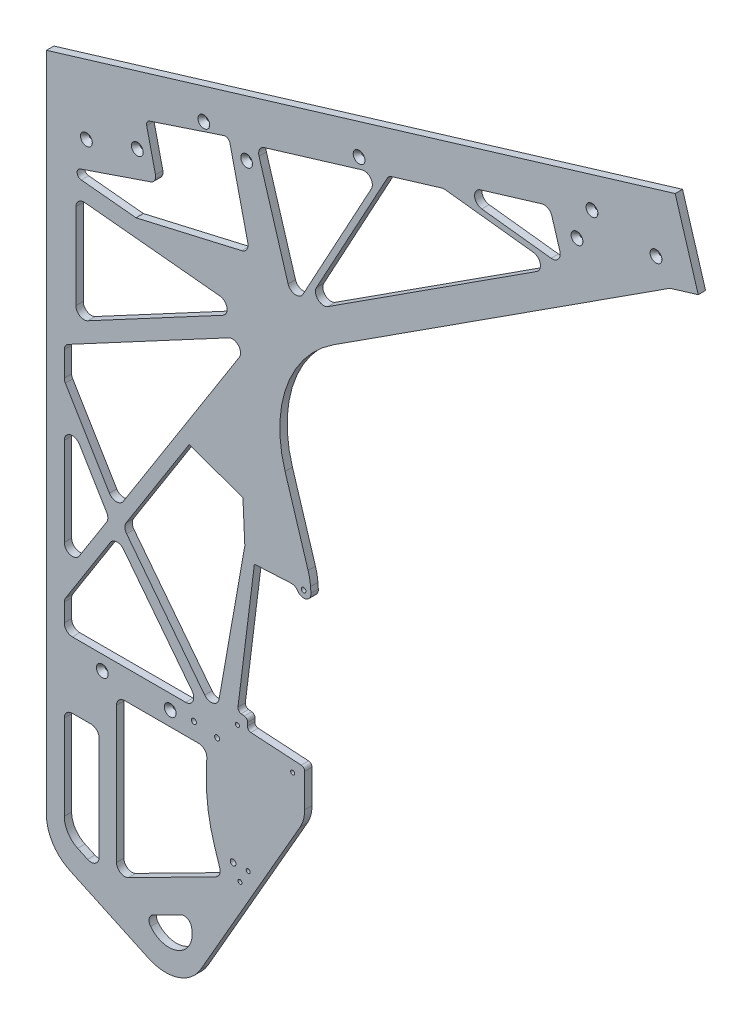
SolidWorks part; units mm, degrees
material "Beech"
ref_plane "Front Plane" through (0, 0, 0) normal (0, 0, 1) x (1, 0, 0)
ref_plane "Top Plane" through (0, 0, 0) normal (0, 1, 0) x (1, 0, 0)
ref_plane "Right Plane" through (0, 0, 0) normal (1, 0, 0) x (0, 0, -1)
sketch "Sketch1" plane through (0, 0, 0) normal (0, 0, 1) x (1, 0, 0)
  line L3 (-17.0528, -329.4943) -> (-52.061, -347.2658)
  line L9 (-123, -235.7894) -> (-123, -309.0696)
  line L10 (-100, -228.7894) -> (-116, -228.7894)
  line L11 (-93, -324.8124) -> (-93, -235.7894)
  line L12 (-111.4524, -327.1958) -> (-102.9583, -331.1566)
  line L20 (84, -200.7842) -> (84, -172.0664)
  line L21 (81.0197, -168.8973) -> (37.7062, -166.2368)
  line L23 (81.0197, -168.8973) -> (37.7062, -166.2368)
  line L24 (89.4313, -36.4853) -> (89.0709, -31.7487)
  line L25 (86.9733, -20.7388) -> (67.1502, 43.2142)
  line L39 (109.0999, 158.659) -> (398.6241, 345.5216)
  line L40 (398.6241, 345.5216) -> (422.935, 352.8794)
  line L46 (422.935, 352.8794) -> (403.0991, 418.4193)
  line L47 (403.0991, 418.4193) -> (-138.3789, 254.5381)
  line L48 (-138.3789, 254.5381) -> (-138.3789, -315.4534)
  line L49 (-118.2139, -347.1062) -> (-50.5059, -378.6789)
  line L50 (-5.4671, -364.4315) -> (80.009, -215.7351)
  line L55 (84, -200.7842) -> (84, -172.0664)
  line L62 (89.4313, -36.4853) -> (89.0709, -31.7487)
  line L63 (86.9733, -20.7388) -> (67.1502, 43.2142)
  line L64 (109.0999, 158.659) -> (398.6241, 345.5216)
  line L65 (398.6241, 345.5216) -> (422.935, 352.8794)
  line L66 (422.935, 352.8794) -> (403.0991, 418.4193)
  line L67 (403.0991, 418.4193) -> (-138.3789, 254.5381)
  line L68 (-138.3789, 254.5381) -> (-138.3789, -315.4534)
  line L69 (-61.1998, 168.1794) -> (29.8266, 189.1945)
  line L70 (-108.3476, 172.8251) -> (-61.1998, 168.1794)
  line L71 (-43.1791, 203.129) -> (-109.2468, 180.5917)
  line L72 (-52.0322, 241.4762) -> (-43.1791, 203.129)
  line L73 (14.4833, 267.3378) -> (-49.3928, 246.173)
  line L74 (35.0726, 197.5898) -> (19.6388, 264.4406)
  line L75 (-102.6958, 70.6213) -> (13.5473, 132.8622)
  line L76 (-113, 150.4873) -> (-113, 76.7923)
  line L77 (10.9295, 145.9995) -> (-105.3136, 157.4535)
  line L78 (-118.2139, -347.1062) -> (-50.5059, -378.6789)
  line L79 (-5.4671, -364.4315) -> (80.009, -215.7351)
  line L81 (-123, -28.6549) -> (-123, -104.7468)
  line L82 (-86.4916, -64.103) -> (-110.0027, -25.0448)
  line L83 (-110.0903, -108.4986) -> (-86.5792, -71.4649)
  line L91 (-78, -203.7894) -> (-78, -320.9929)
  line L92 (-7.2478, -196.7894) -> (-71, -196.7894)
  line L93 (-0.5975, -217.2122) -> (-0.2502, -203.9729)
  line L94 (10.9062, -280.6638) -> (6.4944, -266.8845)
  line L95 (-67.8314, -327.2347) -> (7.4081, -289.0401)
  line L97 (43.2335, -2.4917) -> (44.321, -25.8402) construction
  line L98 (69.3512, -23.7337) -> (62.886, 0.5467) construction
  line L99 (47.5047, -28.6948) -> (66.6392, -27.4998) construction
  line L107 (-15.4708, 21.8839) -> (-69.6883, -63.5168)
  line L108 (30.8453, 5.5646) -> (-15.4708, 21.8839)
  line L109 (32.4846, -29.6329) -> (30.8453, 5.5646)
  line L110 (10.3168, -155.1041) -> (32.4846, -29.6329)
  line L111 (-69.3092, -71.5595) -> (-2.1071, -158.1772)
  line L115 (-83.3585, -85.0495) -> (-123, -147.491)
  line L116 (-12.9629, -160.4984) -> (-71.9182, -84.5103)
  line L117 (-116, -171.7894) -> (-18.4936, -171.7894)
  line L118 (-123, -147.491) -> (-123, -164.7894)
  line L123 (18.5117, 118.5054) -> (-123, 42.7347)
  line L124 (-72.2002, -48.8158) -> (27.7256, 108.5825)
  line L125 (-123, 15.9373) -> (-84.1071, -48.674)
  line L126 (-123, 42.7347) -> (-123, 15.9373)
  line L166 (26.578, -152.854) -> (40.7015, -39.1783)
  line L183 (26.578, -152.854) -> (40.7015, -39.1783)
  line L184 (40.7015, -39.1783) -> (72.3075, -37.5674)
  line L185 (40.7015, -39.1783) -> (72.3075, -37.5674)
  line L240 (34.7318, -162.8731) -> (34.9029, -160.088)
  line L241 (34.7318, -162.8731) -> (34.9029, -160.088)
  line L242 (32.1253, -156.7426) -> (29.3373, -156.3962)
  line L243 (32.1253, -156.7426) -> (29.3373, -156.3962)
  circle A2 centre (83.098, -37.255) radius 2
  arc A4 (-52.061, -347.2658) -> (-17.0528, -329.4943) centre (-32.8243, -341.7931) ccw
  arc A20 (-123, -309.0696) -> (-111.4524, -327.1958) centre (-103, -309.0696) ccw
  arc A21 (-116, -228.7894) -> (-123, -235.7894) centre (-116, -235.7894) ccw
  arc A22 (-93, -235.7894) -> (-100, -228.7894) centre (-100, -235.7894) ccw
  arc A23 (-102.9583, -331.1566) -> (-93, -324.8124) centre (-100, -324.8124) ccw
  arc A31 (89.0709, -31.7487) -> (86.9733, -20.7388) centre (39.215, -35.5422) ccw
  arc A34 (109.0999, 158.659) -> (67.1502, 43.2142) centre (164.1952, 73.2946) ccw
  arc A35 (-138.3789, -315.4534) -> (-118.2139, -347.1062) centre (-103.4539, -315.4534) ccw
  arc A36 (-50.5059, -378.6789) -> (-5.4671, -364.4315) centre (-35.746, -347.0261) ccw
  arc A37 (80.009, -215.7351) -> (84, -200.7842) centre (54, -200.7842) ccw
  arc A46 (29.8266, 189.1945) -> (35.0726, 197.5898) centre (28.252, 196.0151) ccw
  arc A47 (-109.2468, 180.5917) -> (-108.3476, 172.8251) centre (-107.9554, 176.8059) ccw
  arc A48 (-49.3928, 246.173) -> (-52.0322, 241.4762) centre (-48.1347, 242.376) ccw
  arc A49 (19.6388, 264.4406) -> (14.4833, 267.3378) centre (15.7414, 263.5408) ccw
  arc A50 (89.0709, -31.7487) -> (86.9733, -20.7388) centre (39.215, -35.5422) ccw
  arc A51 (109.0999, 158.659) -> (67.1502, 43.2142) centre (164.1952, 73.2946) ccw
  arc A52 (13.5473, 132.8622) -> (10.9295, 145.9995) centre (10.2431, 139.0332) ccw
  arc A53 (-113, 76.7923) -> (-102.6958, 70.6213) centre (-106, 76.7923) ccw
  arc A54 (-105.3136, 157.4535) -> (-113, 150.4873) centre (-106, 150.4873) ccw
  arc A55 (-138.3789, -315.4534) -> (-118.2139, -347.1062) centre (-103.4539, -315.4534) ccw
  arc A56 (-50.5059, -378.6789) -> (-5.4671, -364.4315) centre (-35.746, -347.0261) ccw
  arc A57 (80.009, -215.7351) -> (84, -200.7842) centre (54, -200.7842) ccw
  arc A58 (-110.0027, -25.0448) -> (-123, -28.6549) centre (-116, -28.6549) ccw
  arc A59 (-86.5792, -71.4649) -> (-86.4916, -64.103) centre (-92.4888, -67.7131) ccw
  arc A60 (-123, -104.7468) -> (-110.0903, -108.4986) centre (-116, -104.7468) ccw
  arc A68 (-78, -320.9929) -> (-67.8314, -327.2347) centre (-71, -320.9929) ccw
  arc A69 (-71, -196.7894) -> (-78, -203.7894) centre (-71, -203.7894) ccw
  arc A70 (-0.2502, -203.9729) -> (-7.2478, -196.7894) centre (-7.2478, -203.7894) ccw
  arc A71 (-0.5975, -217.2122) -> (6.4944, -266.8845) centre (149.3509, -221.1459) ccw
  arc A72 (7.4081, -289.0401) -> (10.9062, -280.6638) centre (4.2395, -282.7983) ccw
  arc A74 (44.321, -25.8402) -> (47.5047, -28.6948) centre (47.3177, -25.7007) ccw construction
  arc A75 (62.886, 0.5467) -> (43.2335, -2.4917) centre (53.2227, -2.0264) ccw construction
  arc A76 (66.6392, -27.4998) -> (69.3512, -23.7337) centre (66.4522, -24.5056) ccw construction
  arc A78 (-69.6883, -63.5168) -> (-69.3092, -71.5595) centre (-63.7786, -67.2686) ccw
  arc A79 (-2.1071, -158.1772) -> (10.3168, -155.1041) centre (3.4235, -153.8863) ccw
  arc A84 (-71.9182, -84.5103) -> (-83.3585, -85.0495) centre (-77.4488, -88.8013) ccw
  arc A85 (-18.4936, -171.7894) -> (-12.9629, -160.4984) centre (-18.4936, -164.7894) ccw
  arc A86 (-123, -164.7894) -> (-116, -171.7894) centre (-116, -164.7894) ccw
  arc A88 (27.7256, 108.5825) -> (18.5117, 118.5054) centre (21.8159, 112.3343) ccw
  arc A89 (-84.1071, -48.674) -> (-72.2002, -48.8158) centre (-78.1098, -45.064) ccw
  arc A122 (84, -172.0664) -> (81.0197, -168.8973) centre (80.825, -172.0664) ccw
  arc A123 (84, -172.0664) -> (81.0197, -168.8973) centre (80.825, -172.0664) ccw
  arc A126 (77.9448, -40.4332) -> (83.5751, -43.2993) centre (83.2589, -36.9572) ccw
  arc A127 (77.9448, -40.4332) -> (83.5751, -43.2993) centre (83.2589, -36.9572) ccw
  arc A128 (83.5751, -43.2993) -> (89.4313, -36.4853) centre (83.0996, -36.9671) ccw
  arc A129 (83.5751, -43.2993) -> (89.4313, -36.4853) centre (83.0996, -36.9671) ccw
  arc A136 (77.9448, -40.4332) -> (72.3075, -37.5674) centre (72.6307, -43.9092) ccw
  arc A137 (77.9448, -40.4332) -> (72.3075, -37.5674) centre (72.6307, -43.9092) ccw
  arc A162 (34.7318, -162.8731) -> (37.7062, -166.2368) centre (37.9008, -163.0678) ccw
  arc A163 (34.7318, -162.8731) -> (37.7062, -166.2368) centre (37.9008, -163.0678) ccw
  arc A164 (34.9029, -160.088) -> (32.1253, -156.7426) centre (31.7338, -159.8934) ccw
  arc A165 (34.9029, -160.088) -> (32.1253, -156.7426) centre (31.7338, -159.8934) ccw
  arc A166 (26.578, -152.854) -> (29.3373, -156.3962) centre (29.7288, -153.2454) ccw
  arc A167 (26.578, -152.854) -> (29.3373, -156.3962) centre (29.7288, -153.2454) ccw
  line B0 (236.5506, 323.6498) -> (296.3216, 316.7428)
  line B1 (288.1657, 353.2968) -> (235.3263, 337.3033)
  line B2 (303.8249, 325.7244) -> (296.8934, 348.6248)
  line B3 (104.1239, 184.6459) -> (283.8662, 300.6596)
  line B4 (156.4343, 308.2003) -> (94.1802, 193.8748)
  line B5 (203.4752, 322.4386) -> (156.4343, 308.2003)
  line B6 (280.8737, 313.4946) -> (203.4752, 322.4386)
  line B7 (44.7058, 267.0687) -> (69.7399, 184.3604)
  line B8 (133.2777, 301.1913) -> (49.3777, 275.7965)
  line B9 (82.5874, 183.0407) -> (141.4532, 291.1438)
  arc B10 (296.3216, 316.7428) -> (303.8249, 325.7244) centre (297.1251, 323.6965) ccw
  arc B11 (235.3263, 337.3033) -> (236.5506, 323.6498) centre (237.3542, 330.6035) ccw
  arc B12 (296.8934, 348.6248) -> (288.1657, 353.2968) centre (290.1936, 346.5969) ccw
  arc B13 (283.8662, 300.6596) -> (280.8737, 313.4946) centre (280.0701, 306.5409) ccw
  arc B14 (94.1802, 193.8748) -> (104.1239, 184.6459) centre (100.3278, 190.5272) ccw
  arc B15 (69.7399, 184.3604) -> (82.5874, 183.0407) centre (76.4398, 186.3883) ccw
  arc B16 (49.3777, 275.7965) -> (44.7058, 267.0687) centre (51.4056, 269.0966) ccw
  arc B17 (141.4532, 291.1438) -> (133.2777, 301.1913) centre (135.3056, 294.4914) ccw
  dimension "D1" = 0
sketch_block_instance "Block1-1"
sketch_block "Block1"
extrude "Boss-Extrude1" add sketch "Sketch1" along normal blind 6.35
hole_wizard "#8 Clearance Hole1" positions "Sketch2" profile "Sketch3" hole size "#8" standard "ANSI Inch" end condition through all
sketch "Sketch2" plane through (0, 0, 6.35) normal (0, 0, 1) x (1, 0, 0)
  point P0 (22.4173, -270.7692)
sketch "Sketch3" plane through (22.4173, -270.7692, 6.35) normal (1, 0, 0) x (0, -1, 0)
  line L0 (0, 0) -> (0, 6.35)
  line L1 (0, 6.35) -> (2.4574, 6.35)
  line L2 (2.4574, 6.35) -> (2.4574, 0)
  line L5 (2.4574, 0) -> (0, 0)
  line L11 (0, -6.35) -> (0, 107.95) construction
  dimension "Thru Hole Dia." = 4.9149
  dimension "Thru Hole Depth" = 6.35
hole_wizard "#29 (0.136) Diameter Hole1" positions "Sketch4" profile "Sketch5" hole size "#29" standard "ANSI Inch" end condition through all
sketch "Sketch4" plane through (0, 0, 6.35) normal (0, 0, 1) x (1, 0, 0)
  point P0 (28.3036, -282.3356)
  point P5 (35.3953, -270.7692)
  point P9 (26.0849, -166.3788)
  point P12 (73.6862, -178.0913)
sketch "Sketch5" plane through (28.3036, -282.3356, 6.35) normal (1, 0, 0) x (0, -1, 0)
  line L0 (0, 0) -> (0, 6.35)
  line L1 (0, 6.35) -> (1.7272, 6.35)
  line L2 (1.7272, 6.35) -> (1.7272, 0)
  line L5 (1.7272, 0) -> (0, 0)
  line L11 (0, -6.35) -> (0, 107.95) construction
  dimension "Thru Hole Dia." = 3.4544
  dimension "Thru Hole Depth" = 6.35
fillet "Fillet2" radius 6.35 8 edges at (-17.0528, -329.4943, 3.175) (-52.061, -347.2658, 3.175) (-123, -147.491, 3.175) (-123, 15.9373, 3.175) (-123, 42.7347, 3.175) (-43.1791, 203.129, 3.175) (156.4343, 308.2003, 3.175) (203.4752, 322.4386, 3.175)
hole_wizard "Hole1" positions "Sketch6" profile "Sketch7" legacy
sketch "Sketch6" plane through (-277.2867, -215.2871, 6.35) normal (0, 0, 1) x (-0.09, -0.9959, 0)
  point P4 (-507.0387, 229.7761)
  point P6 (-559.3712, 359.3037)
  point P8 (-637.87, 553.5951)
  point P10 (-636.0712, 609.1114)
  point P12 (-609.4494, 543.2202)
  point P16 (-499.7233, 267.4963)
  point P18 (-453.1036, 177.1887)
  point P20 (-434.4591, 134.8062)
  point P22 (-52.9605, 241.7526)
  point P24 (-47.6978, 183.4898)
sketch "Sketch7" plane through (-2.8292, 269.0251, 6.35) normal (1, 0, 0) x (0, -1, 0)
  line L0 (0, 0) -> (0, 32.7039)
  line L1 (0, 32.7039) -> (1.5875, 31.75)
  line L2 (1.5875, 31.75) -> (1.5875, 4.0177)
  line L3 (1.5875, 4.0177) -> (5.08, 0)
  line L4 (5.08, 0) -> (0, 0)
  line L5 (0, -14.3089) -> (0, 102.4216) construction
  line L6 (0, 32.7039) -> (-1.5875, 31.75) construction
  line L7 (-1.5875, 4.0177) -> (-5.08, 0) construction
  dimension "Diameter" = 3.175
  dimension "Depth" = 31.75
  dimension "C-Sink Diameter" = 10.16
  dimension "C-Sink Angle" = 82
  dimension "Drill Angle" = 118
hole_wizard "#6 Clearance Hole1" positions "Sketch8" profile "Sketch9" hole size "#6" standard "ANSI Inch" end condition up to next
sketch "Sketch8" plane through (0, 0, 6.35) normal (0, 0, 1) x (1, 0, 0)
  point P0 (8.6038, -184.7304)
  point P2 (-11.3597, -182.482)
sketch "Sketch9" plane through (8.6038, -184.7304, 6.35) normal (1, 0, 0) x (0, -1, 0)
  line L0 (0, 0) -> (0, 6.35)
  line L1 (0, 6.35) -> (2.1526, 6.35)
  line L2 (2.1526, 6.35) -> (2.1526, 0)
  line L5 (2.1526, 0) -> (0, 0)
  line L11 (0, -6.35) -> (0, 107.95) construction
  dimension "Thru Hole Dia." = 4.3053
  dimension "Thru Hole Depth" = 6.35
